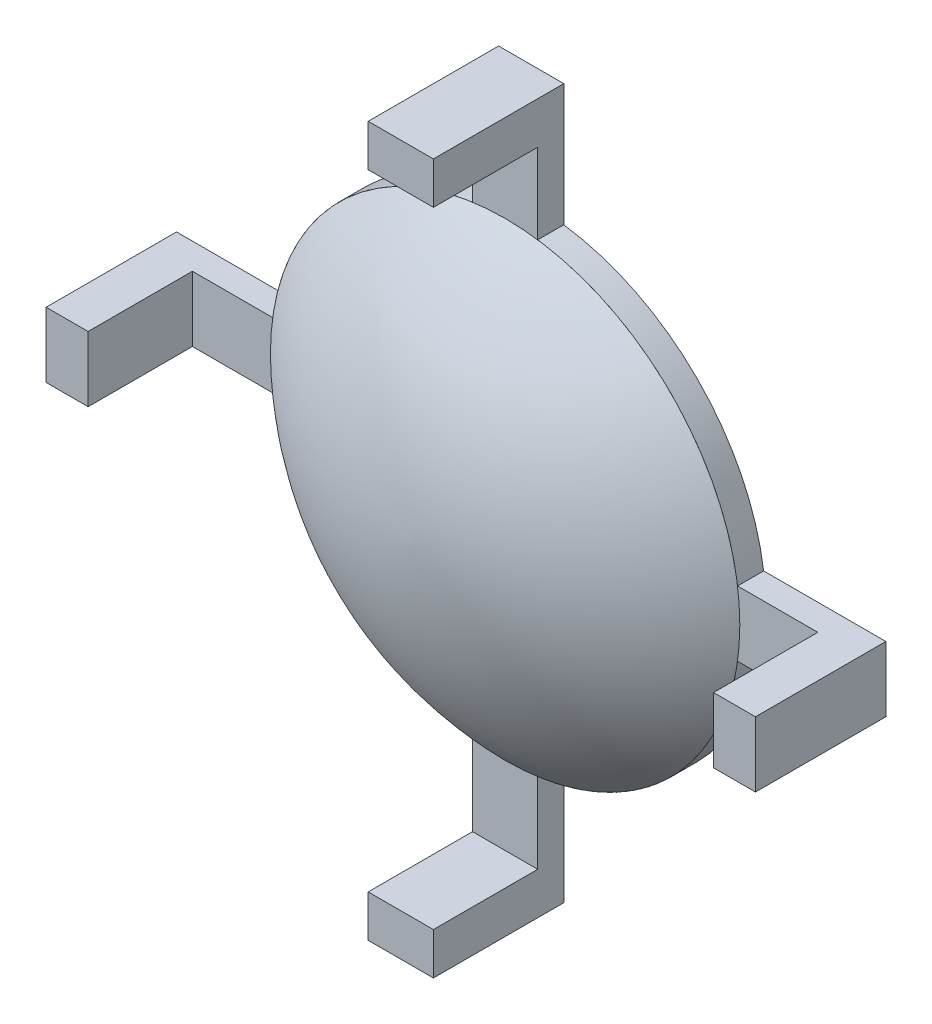
SolidWorks part; units mm, degrees
ref_plane "Front Plane" through (0, 0, 0) normal (0, 0, 1) x (1, 0, 0)
ref_plane "Top Plane" through (0, 0, 0) normal (0, 1, 0) x (1, 0, 0)
ref_plane "Right Plane" through (0, 0, 0) normal (1, 0, 0) x (0, 0, -1)
sketch "Sketch1" plane through (0, 0, 0) normal (0, 0, 1) x (1, 0, 0)
  line L0 (0, -55) -> (0, 55) construction
  line L1 (-13.6, -1.25) -> (13.6, -1.25)
  line L2 (-13.6, -1.25) -> (-13.6, 1.25)
  line L3 (-13.6, 1.25) -> (13.6, 1.25)
  line L4 (13.6, -1.25) -> (13.6, 1.25)
  line L5 (-13.6, -1.25) -> (13.6, 1.25) construction
  line L6 (-13.6, 1.25) -> (13.6, -1.25) construction
  line L7 (-1.25, 13.6) -> (1.25, 13.6)
  line L8 (-1.25, 13.6) -> (-1.25, -13.6)
  line L9 (-1.25, -13.6) -> (1.25, -13.6)
  line L10 (1.25, 13.6) -> (1.25, -13.6)
  line L11 (13.6, 1.25) -> (13.6, -1.25)
  line L12 (13.6, 1.25) -> (-13.6, 1.25)
  line L13 (-13.6, 1.25) -> (-13.6, -1.25)
  line L14 (13.6, -1.25) -> (-13.6, -1.25)
  line L15 (1.25, -13.6) -> (-1.25, -13.6)
  line L16 (1.25, -13.6) -> (1.25, 13.6)
  line L17 (1.25, 13.6) -> (-1.25, 13.6)
  line L18 (-1.25, -13.6) -> (-1.25, 13.6)
  circle A0 centre (0, 0) radius 9
  point P22 (0, 0)
  dimension "D1" = 27.2
  dimension "D2" = 18
  dimension "D3" = 0
  dimension "D4" = 2.5
  dimension "D5" = 4
extrude "Boss-Extrude1" add sketch "Sketch1" along normal blind 1 contours A0 L3 L2 L1 | A0 L14 L4 L12 | L15 L18 L17 L16
sketch "Sketch2" plane through (0, 0, 1) normal (0, 0, 1) x (1, 0, 0)
  line L0 (-13.6, 1.25) -> (-8.9128, 1.25) construction
  line L1 (-13.6, 1.25) -> (-11.9906, 1.25)
  line L2 (-13.6, 1.25) -> (-13.6, -1.25)
  line L3 (-13.6, -1.25) -> (-11.9906, -1.25)
  line L4 (-11.9906, 1.25) -> (-11.9906, -1.25)
  line L5 (1.25, 13.6) -> (-1.25, 13.6)
  line L6 (1.25, 13.6) -> (1.25, 11.9906)
  line L7 (1.25, 11.9906) -> (-1.25, 11.9906)
  line L8 (-1.25, 13.6) -> (-1.25, 11.9906)
  line L9 (13.6, -1.25) -> (13.6, 1.25)
  line L10 (13.6, -1.25) -> (11.9906, -1.25)
  line L11 (11.9906, -1.25) -> (11.9906, 1.25)
  line L12 (13.6, 1.25) -> (11.9906, 1.25)
  line L13 (-1.25, -13.6) -> (1.25, -13.6)
  line L14 (-1.25, -13.6) -> (-1.25, -11.9906)
  line L15 (-1.25, -11.9906) -> (1.25, -11.9906)
  line L16 (1.25, -13.6) -> (1.25, -11.9906)
  point P21 (0, 0)
  dimension "D1" = 2.5
  dimension "D2" = 0
  dimension "D3" = 4
extrude "Boss-Extrude2" add sketch "Sketch2" along normal blind 4
sketch "Sketch7" plane through (0, 0, 0) normal (0, 1, 0) x (1, 0, 0)
  line L0 (-0.0002, 0) -> (-0.0002, -1)
  line L1 (-0.0002, -1) -> (-9.0002, -1)
  line L2 (-0.0002, -1) -> (-0.0002, -4.7)
  line L3 (-0.0002, -4.7) -> (-0.0002, -5.7261) construction
  line L4 (-1.25, 0) -> (-8.9128, 0) construction
  arc A0 (-9.0002, -1) -> (-0.0002, -4.7) centre (0.3185, 8.8712) ccw
  dimension "D4" = 13.5749
  dimension "D1" = 1
  dimension "D2" = 9
  dimension "D3" = 3.7
  dimension "D5" = 1
revolve "Revolve4" add sketch "Sketch7" angle 360 about L3
